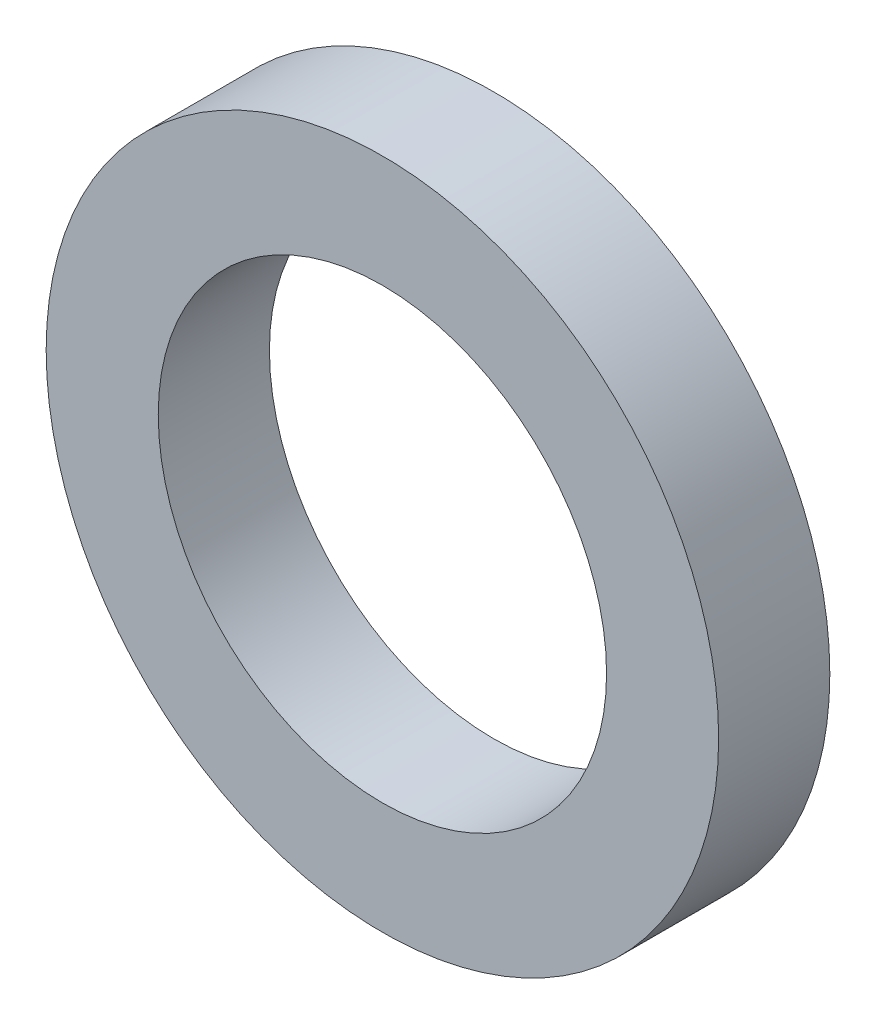
SolidWorks part; units mm, degrees
material "Plain Carbon Steel"
ref_plane "Front Plane" through (0, 0, 0) normal (0, 0, 1) x (1, 0, 0)
ref_plane "Top Plane" through (0, 0, 0) normal (0, 1, 0) x (1, 0, 0)
ref_plane "Right Plane" through (0, 0, 0) normal (1, 0, 0) x (0, 0, -1)
sketch "Sketch1" plane through (0, 0, 0) normal (0, 0, 1) x (1, 0, 0)
  circle A0 centre (0, 0) radius 3.175
  circle A1 centre (0, 0) radius 4.7625
  dimension "D1" = 6.35
  dimension "D2" = 9.525
extrude "Boss-Extrude1" add sketch "Sketch1" along normal blind 1.5748
